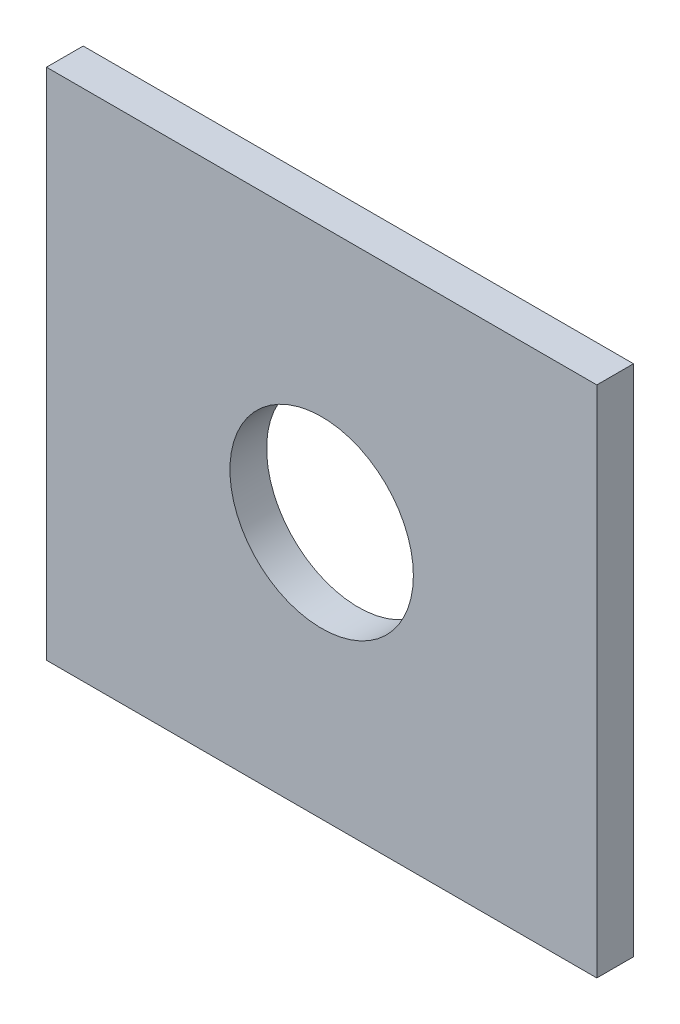
SolidWorks part; units mm, degrees
ref_plane "Front Plane" through (0, 0, 0) normal (0, 0, 1) x (1, 0, 0)
ref_plane "Top Plane" through (0, 0, 0) normal (0, 1, 0) x (1, 0, 0)
ref_plane "Right Plane" through (0, 0, 0) normal (1, 0, 0) x (0, 0, -1)
sketch "Sketch1" plane through (0, 0, 0) normal (0, 0, 1) x (1, 0, 0)
  line L1 (75, -70) -> (-75, -70)
  line L2 (75, -70) -> (75, 70)
  line L3 (75, 70) -> (-75, 70)
  line L4 (-75, -70) -> (-75, 70)
  line L5 (75, -70) -> (-75, 70) construction
  line L6 (75, 70) -> (-75, -70) construction
  circle A0 centre (0, 0) radius 25
  point P0 (0, 0)
  dimension "D3" = 50
  dimension "D1" = 150
  dimension "D2" = 140
extrude "Boss-Extrude1" add sketch "Sketch1" along normal blind 10
